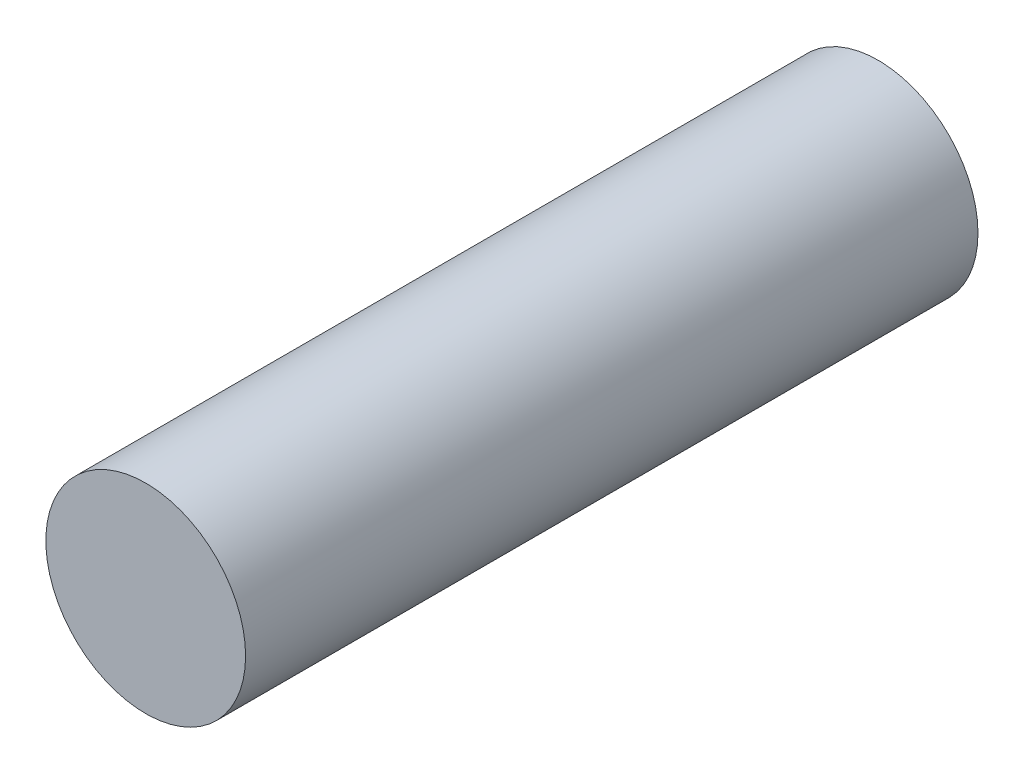
SolidWorks part; units mm, degrees
material "Oak"
ref_plane "Front Plane" through (0, 0, 0) normal (0, 0, 1) x (1, 0, 0)
ref_plane "Top Plane" through (0, 0, 0) normal (0, 1, 0) x (1, 0, 0)
ref_plane "Right Plane" through (0, 0, 0) normal (1, 0, 0) x (0, 0, -1)
sketch "Sketch1" plane through (0, 0, 0) normal (0, 0, 1) x (1, 0, 0)
  circle A0 centre (0, 0) radius 9.525
  dimension "D1" = 19.05
extrude "Boss-Extrude1" add sketch "Sketch1" along normal blind 69.85
